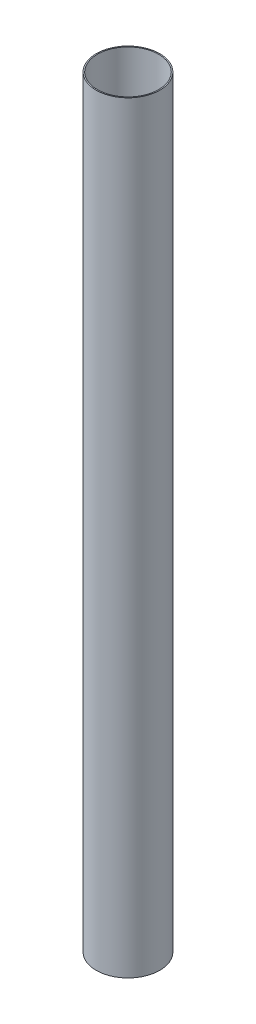
SolidWorks part; units mm, degrees
ref_plane "Front Plane" through (0, 0, 0) normal (0, 0, 1) x (1, 0, 0)
ref_plane "Top Plane" through (0, 0, 0) normal (0, 1, 0) x (1, 0, 0)
ref_plane "Right Plane" through (0, 0, 0) normal (1, 0, 0) x (0, 0, -1)
sketch "Sketch1" plane through (0, 0, 0) normal (0, 1, 0) x (1, 0, 0)
  circle A0 centre (0, 0) radius 41
  circle A1 centre (0, 0) radius 42.5
  dimension "D1" = 1.5
  dimension "D2" = 82
extrude "Boss-Extrude1" add sketch "Sketch1" along normal blind 1020
